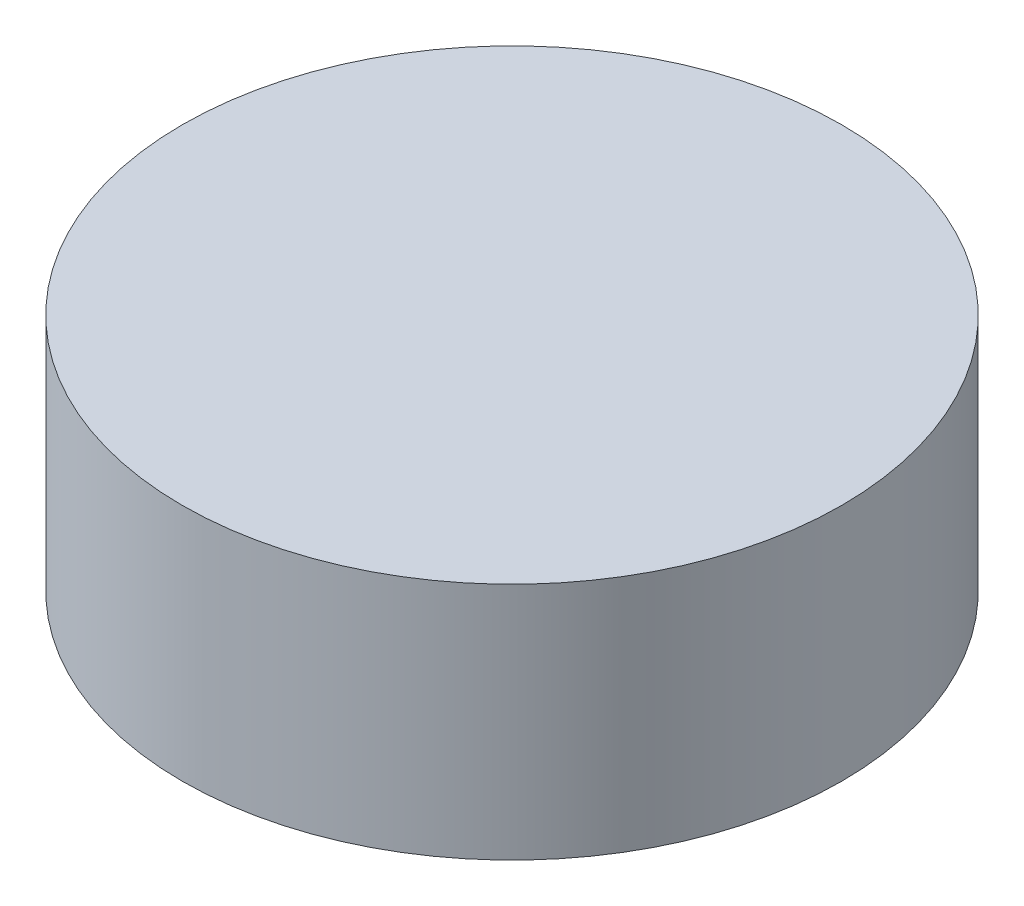
SolidWorks part; units mm, degrees
ref_plane "Front Plane" through (0, 0, 0) normal (0, 0, 1) x (1, 0, 0)
ref_plane "Top Plane" through (0, 0, 0) normal (0, 1, 0) x (1, 0, 0)
ref_plane "Right Plane" through (0, 0, 0) normal (1, 0, 0) x (0, 0, -1)
sketch "Sketch1" plane through (0, 0, 0) normal (0, 1, 0) x (1, 0, 0)
  circle A0 centre (0, 0) radius 13.8
  dimension "D1" = 27.6
extrude "Boss-Extrude1" add sketch "Sketch1" along normal blind 10
